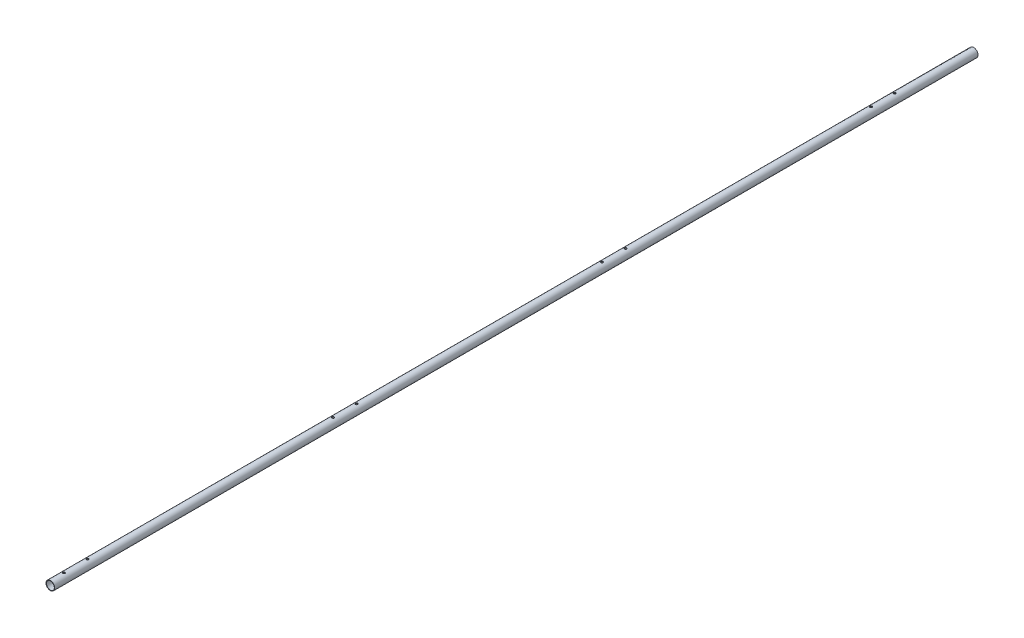
SolidWorks part; units mm, degrees
ref_plane "Front Plane" through (0, 0, 0) normal (0, 0, 1) x (1, 0, 0)
ref_plane "Top Plane" through (0, 0, 0) normal (0, 1, 0) x (1, 0, 0)
ref_plane "Right Plane" through (0, 0, 0) normal (1, 0, 0) x (0, 0, -1)
sketch "Sketch1" plane through (0, 0, 0) normal (0, 0, 1) x (1, 0, 0)
  circle A0 centre (0, 0) radius 10
  dimension "D1" = 20
extrude "Extrude-Thin1" add sketch "Sketch1" along normal blind 2114 thin thin type one direction reverse wall 1
sketch "Sketch2" plane through (0, 0, 0) normal (0, 1, 0) x (1, 0, 0)
  line L0 (0, 0) -> (0, 48.4061) construction
  line L1 (0, -181.1) -> (0, -235.1) construction
  line L2 (0, -208.1) -> (48.7983, -208.1) construction
  line L3 (0, 0) -> (48.7983, 0) construction
  dimension "D1" = 54
  dimension "D2" = 208.1
hole_wizard "#10 Clearance Hole1" positions "3DSketch2" profile "Sketch4" hole size "#10" standard "Ansi Inch"
sketch3d "3DSketch2"
  point P0 (0, 10, 181.1)
  point P1 (0, 10, 235.1)
sketch "Sketch4" plane through (0, 10, 181.1) normal (1, 0, 0) x (0, 0, 1)
  line L0 (0, 0) -> (0, 11.5338)
  line L1 (0, 11.5338) -> (2.5527, 10)
  line L2 (2.5527, 10) -> (2.5527, 0)
  line L5 (2.5527, 0) -> (0, 0)
  line L10 (0, 11.5338) -> (-2.5527, 10) construction
  line L11 (0, -6.35) -> (0, 107.95) construction
  dimension "Hole Dia." = 5.1054
  dimension "Hole Depth" = 10
  dimension "Drill Angle" = 118
pattern_linear "LPattern1" count 4 spacing 616 along (0, 0, 1) of "#10 Clearance Hole1"
